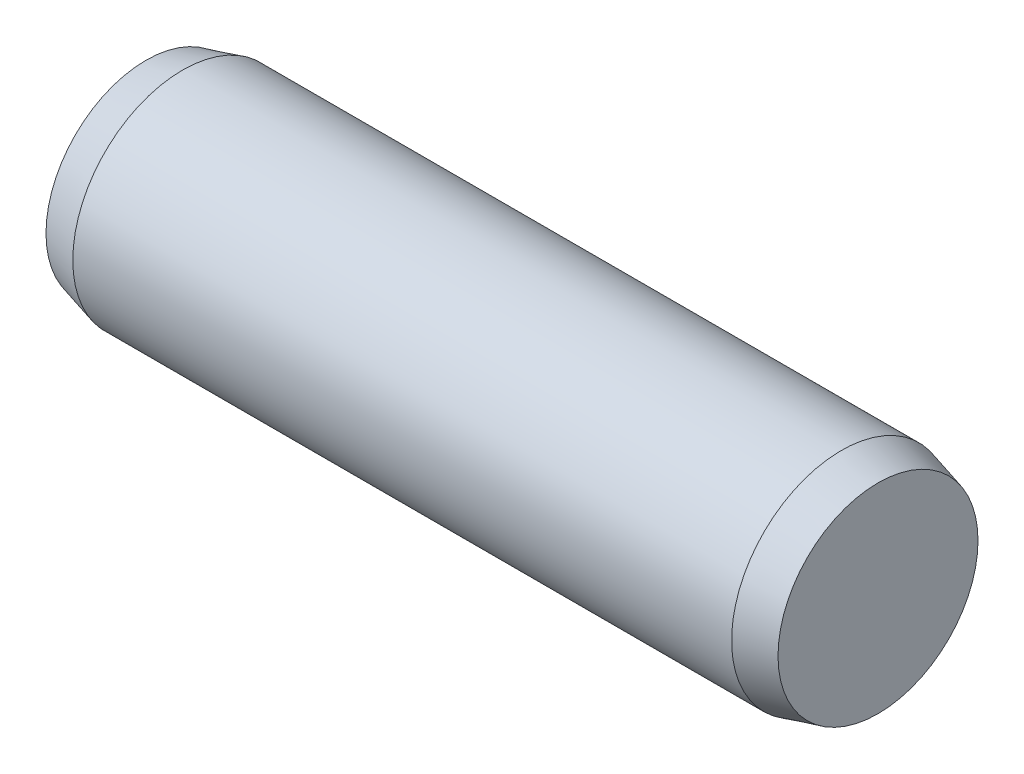
SolidWorks part; units mm, degrees
ref_plane "Front Plane" through (0, 0, 0) normal (0, 0, 1) x (1, 0, 0)
ref_plane "Top Plane" through (0, 0, 0) normal (0, 1, 0) x (1, 0, 0)
ref_plane "Right Plane" through (0, 0, 0) normal (1, 0, 0) x (0, 0, -1)
sketch "Sketch1" plane through (0, 0, 0) normal (0, 0, 1) x (1, 0, 0)
  line L0 (-4.5, 0) -> (4.5, 0) construction
  line L1 (4.5, 1.5) -> (4.5, -1.5) construction
  line L2 (-4.5, 1.5) -> (-4.5, -1.5) construction
  line L3 (5, 1.5) -> (5, -1.5) construction
  line L4 (-5, 1.5) -> (-5, -1.5) construction
  line L5 (-4.5, 0) -> (-5, 0) construction
  line L6 (4.5, 0) -> (5, 0) construction
  dimension "D1" = 0.5
  dimension "Dia" = 3
  dimension "Length" = 10
  dimension "C" = 0.5
sketch "Sketch2" plane through (0, 0, 0) normal (1, 0, 0) x (0, 0, -1)
  circle A0 centre (0, 0) radius 1.5
extrude "Extrude1" add sketch "Sketch2" against normal up to vertex (4.5 mm away) and the other way up to vertex (4.5 mm away) up to point (-4.5, 1.5, 0) other way up to point (4.5, 1.5, 0)
sketch "Sketch3" plane through (4.5, 0, 0) normal (1, 0, 0) x (0, 0, -1)
  circle A1 centre (0, 0) radius 1.5
  circle A2 centre (0, 0) radius 1.5
  dimension "D1" = 0
extrude "Extrude2" add sketch "Sketch3" along normal up to vertex (0.5 mm away) draft 15 up to point (5, 0, 0)
sketch "Sketch4" plane through (-4.5, 0, 0) normal (-1, 0, 0) x (0, 0, 1)
  circle A1 centre (0, 0) radius 1.5
  circle A2 centre (0, 0) radius 1.5
  dimension "D1" = 0
extrude "Extrude3" add sketch "Sketch4" along normal up to vertex (0.5 mm away) draft 15 up to point (-5, 0, 0)
equation "\"D1@Sketch1\" = \"C@Sketch1\""
